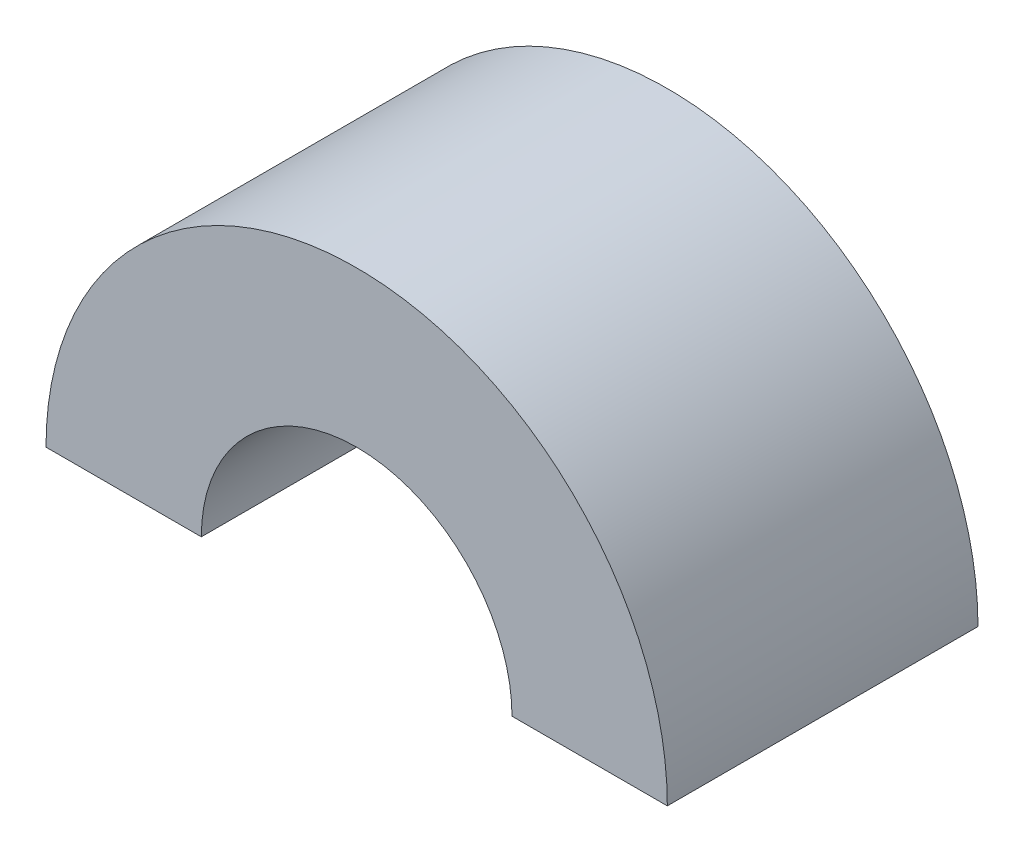
SolidWorks part; units mm, degrees
material "AISI 1020 Steel, Cold Rolled"
ref_plane "Front Plane" through (0, 0, 0) normal (0, 0, 1) x (1, 0, 0)
ref_plane "Top Plane" through (0, 0, 0) normal (0, 1, 0) x (1, 0, 0)
ref_plane "Right Plane" through (0, 0, 0) normal (1, 0, 0) x (0, 0, -1)
sketch "Sketch1" plane through (0, 0, 0) normal (0, 0, 1) x (1, 0, 0)
  line L0 (-15, 0) -> (-7.5, 0)
  line L1 (7.5, 0) -> (15, 0)
  arc A0 (-15, 0) -> (15, 0) centre (0, 0) cw
  arc A1 (-7.5, 0) -> (7.5, 0) centre (0, 0) cw
  dimension "D1" = 15
  dimension "D2" = 7.5
extrude "Boss-Extrude1" add sketch "Sketch1" along normal blind 15
chamfer "Chamfer1" [suppressed] distance 0.5 angle 45
